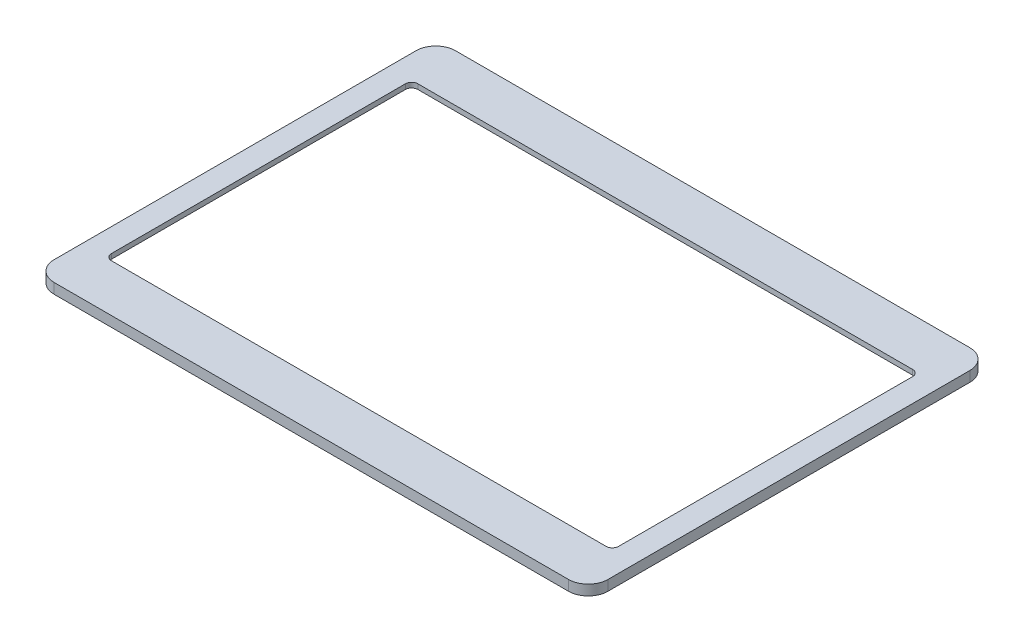
SolidWorks part; units mm, degrees
ref_plane "Front Plane" through (0, 0, 0) normal (0, 0, 1) x (1, 0, 0)
ref_plane "Top Plane" through (0, 0, 0) normal (0, 1, 0) x (1, 0, 0)
ref_plane "Right Plane" through (0, 0, 0) normal (1, 0, 0) x (0, 0, -1)
sketch "Sketch1" plane through (0, 0, 0) normal (0, 1, 0) x (1, 0, 0)
  line L1 (-82.65, 64.5) -> (82.65, 64.5)
  line L2 (-89, 58.15) -> (-89, -58.15)
  line L3 (-82.65, -64.5) -> (82.65, -64.5)
  line L4 (89, 58.15) -> (89, -58.15)
  line L5 (-89, 64.5) -> (89, -64.5) construction
  line L6 (-89, -64.5) -> (89, 64.5) construction
  line L7 (-79.5, 49.25) -> (79.5, 49.25)
  line L8 (-81.5, 47.25) -> (-81.5, -47.25)
  line L9 (-79.5, -49.25) -> (79.5, -49.25)
  line L10 (81.5, 47.25) -> (81.5, -47.25)
  arc A0 (-79.5, 49.25) -> (-81.5, 47.25) centre (-79.5, 47.25) ccw
  arc A1 (-79.5, -49.25) -> (-81.5, -47.25) centre (-79.5, -47.25) cw
  arc A2 (79.5, -49.25) -> (81.5, -47.25) centre (79.5, -47.25) ccw
  arc A3 (81.5, 47.25) -> (79.5, 49.25) centre (79.5, 47.25) ccw
  arc A4 (-89, 58.15) -> (-82.65, 64.5) centre (-82.65, 58.15) cw
  arc A5 (-89, -58.15) -> (-82.65, -64.5) centre (-82.65, -58.15) ccw
  arc A6 (89, 58.15) -> (82.65, 64.5) centre (82.65, 58.15) ccw
  arc A7 (82.65, -64.5) -> (89, -58.15) centre (82.65, -58.15) ccw
  point P0 (0, 0)
  point P12 (-81.5, 49.25)
  point P15 (-81.5, -49.25)
  point P20 (81.5, 49.25)
  dimension "D7" = 2
  dimension "D8" = 2
  dimension "D9" = 2
  dimension "D10" = 2
  dimension "D11" = 6.35
  dimension "D12" = 6.35
  dimension "D13" = 6.35
  dimension "D14" = 6.35
  dimension "D1" = 129
  dimension "D2" = 178
  dimension "D3" = 163
  dimension "D4" = 98.5
  dimension "D5" = 7.5
  dimension "D6" = 15.25
extrude "Outside-extrude" add sketch "Sketch1" along normal blind 3.3
sketch "Sketch2" plane through (0, 0, 0) normal (0, 1, 0) x (1, 0, 0)
  line L0 (-15.5, -58.5) -> (-15.5, -60.5)
  line L1 (-85.5, 53.5) -> (85.5, 53.5)
  line L2 (-85.5, 53.5) -> (-85.5, -58.5)
  line L4 (85.5, 53.5) -> (85.5, -58.75)
  line L5 (-85.5, 53.5) -> (85.5, -58.75) construction
  line L6 (-85.5, -58.5) -> (85.5, 53.5) construction
  line L7 (-15.5, -60.5) -> (15.5, -60.5)
  line L8 (15.5, -60.5) -> (15.5, -58.75)
  line L9 (-85.5, -58.5) -> (-15.5, -58.5)
  line L10 (15.5, -58.75) -> (85.5, -58.75)
  line L13 (82.65, 64.5) -> (-82.65, 64.5) construction
  point P0 (0, 0)
  dimension "D1" = 171
  dimension "D2" = 112
  dimension "D3" = 70
  dimension "D4" = 70
  dimension "D5" = 2
  dimension "D6" = 11
extrude "Cut-Extrude4" cut sketch "Sketch2" along normal blind 1.7
